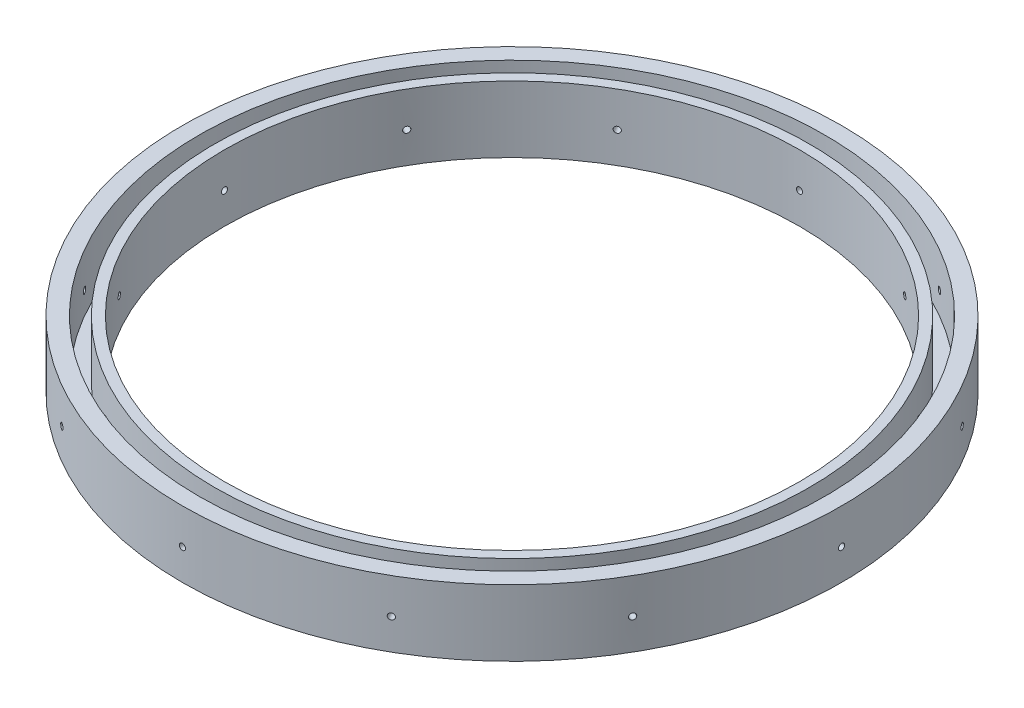
SolidWorks part; units mm, degrees
ref_plane "Front Plane" through (0, 0, 0) normal (0, 0, 1) x (1, 0, 0)
ref_plane "Top Plane" through (0, 0, 0) normal (0, 1, 0) x (1, 0, 0)
ref_plane "Right Plane" through (0, 0, 0) normal (1, 0, 0) x (0, 0, -1)
sketch "Sketch1" plane through (0, 0, 0) normal (0, 1, 0) x (1, 0, 0)
  circle A0 centre (0, 0) radius 94.615
  circle A1 centre (0, 0) radius 82.55
  dimension "D1" = 189.23
  dimension "D2" = 165.1
extrude "Boss-Extrude1" add sketch "Sketch1" along normal blind 19.05
sketch "Sketch2" plane through (0, 19.05, 0) normal (0, 1, 0) x (1, 0, 0)
  circle A0 centre (0, 0) radius 85.4075
  circle A1 centre (0, 0) radius 89.8525
  dimension "D1" = 179.705
  dimension "D2" = 170.815
extrude "Cut-Extrude1" cut sketch "Sketch2" against normal blind 16.51
sketch "Sketch3" plane through (0, 0, 0) normal (0, 0, 1) x (1, 0, 0)
  line L0 (94.615, 19.05) -> (-94.615, 19.05) construction
  circle A0 centre (0, 8.89) radius 0.875
  dimension "D1" = 1.75
  dimension "D2" = 10.16
extrude "Cut-Extrude2" cut sketch "Sketch3" against normal up to surface (94.611 mm away)
pattern_circular "CirPattern1" count 12 over 360 about axis through (0, 19.05, 0) along (0, 1, 0) of "Cut-Extrude2"
